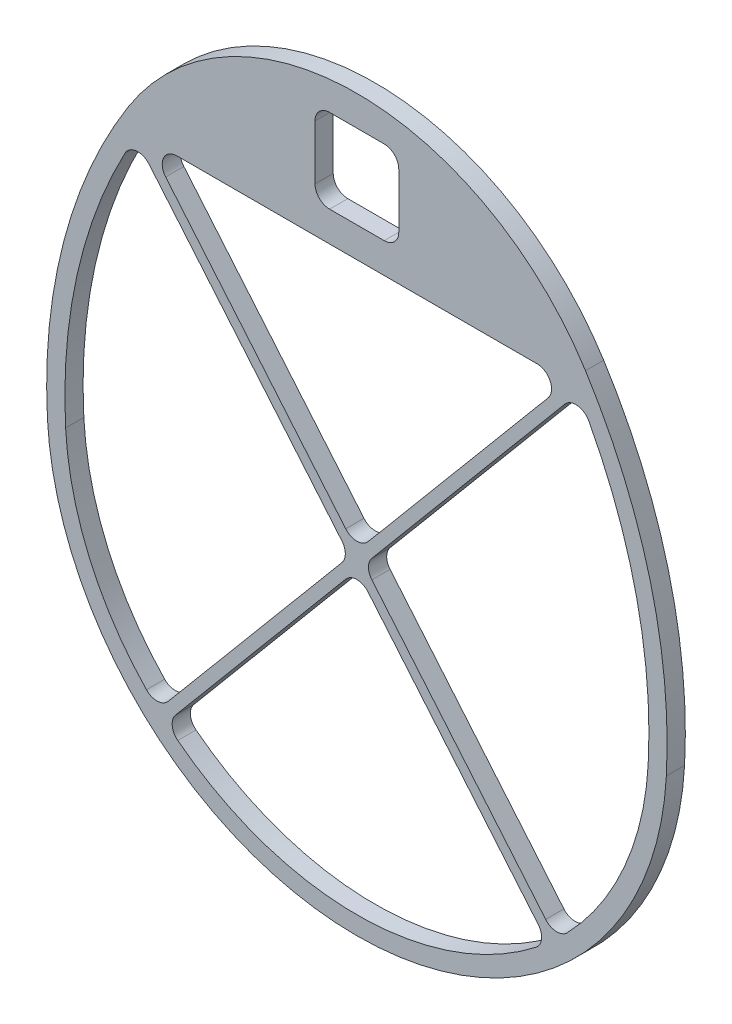
SolidWorks part; units mm, degrees
material "Balsa"
ref_plane "Front Plane" through (0, 0, 0) normal (0, 0, 1) x (1, 0, 0)
ref_plane "Top Plane" through (0, 0, 0) normal (0, 1, 0) x (1, 0, 0)
ref_plane "Right Plane" through (0, 0, 0) normal (1, 0, 0) x (0, 0, -1)
sketch "Sketch1" plane through (0, 0, 0) normal (0, 0, 1) x (1, 0, 0)
  line L8 (-101.6, 0) -> (101.6, 0) construction
  line L9 (-79.7395, 107.95) -> (79.7395, 107.95)
  line L10 (-76.2, 101.6) -> (76.2, 101.6)
  line L21 (-107.9408, -0.3425) -> (-101.6, 0)
  line L22 (101.6, 0) -> (107.9408, -0.3425)
  arc A0 (76.2, 101.6) -> (101.6, 0) centre (-75.9412, 9.5897) cw
  arc A1 (-76.2, 101.6) -> (-101.6, 0) centre (75.9412, 9.5897) ccw
  arc A2 (-79.7395, 107.95) -> (-107.9408, -0.3425) centre (75.9412, 9.5897) ccw
  arc A3 (79.7395, 107.95) -> (107.9408, -0.3425) centre (-75.9412, 9.5897) cw
  arc A4 (-81.6336, 104.8861) -> (-107.9408, -0.3425) centre (75.9412, 9.5897) ccw construction
  arc A5 (81.6336, 104.8861) -> (107.9408, -0.3425) centre (-75.9412, 9.5897) cw construction
  arc A6 (76.2, 101.6) -> (101.6, 0) centre (-75.9412, 9.5897) cw construction
  arc A7 (-76.2, 101.6) -> (-101.6, 0) centre (75.9412, 9.5897) ccw construction
  arc A8 (-79.7395, 107.95) -> (79.7395, 107.95) centre (0, 57.57) cw
  arc A9 (-101.6, 0) -> (101.6, 0) centre (0, 5.4878) ccw
  arc A10 (-107.9408, -0.3425) -> (107.9408, -0.3425) centre (0, 5.4878) ccw
  point P0 (0, 0)
  point P13 (0, 101.6)
  dimension "D7" = 203.2
  dimension "D2" = 177.8
  dimension "D3" = 101.6
  dimension "D6" = 152.4
  dimension "D1" = 6.35
  dimension "D4" = 6.35
  dimension "D5" = 6.35
extrude "Boss-Extrude1" add sketch "Sketch1" along normal blind 6.35
sketch "Sketch2" plane through (0, 0, 6.35) normal (0, 0, 1) x (1, 0, 0)
  line L0 (0, 101.6) -> (0, 151.8914) construction
  line L1 (-14.605, 141.3507) -> (14.605, 141.3507)
  line L2 (-14.605, 141.3507) -> (-14.605, 112.1407)
  line L3 (-14.605, 112.1407) -> (14.605, 112.1407)
  line L4 (14.605, 141.3507) -> (14.605, 112.1407)
  line L5 (-14.605, 141.3507) -> (14.605, 112.1407) construction
  line L6 (-14.605, 112.1407) -> (14.605, 141.3507) construction
  line L7 (-76.2, 101.6) -> (76.2, 101.6) construction
  arc A0 (79.7395, 107.95) -> (-79.7395, 107.95) centre (0, 57.57) ccw construction
  point P0 (0, 126.7457)
  point P15 (0, 126.7457)
  dimension "D1" = 29.21
  dimension "D2" = 29.21
extrude "Cut-Extrude1" cut sketch "Sketch2" against normal up to next
fillet "Fillet1" radius 5.08 4 edges at (14.605, 112.1407, 3.175) (14.605, 141.3507, 3.175) (-14.605, 141.3507, 3.175) (-14.605, 112.1407, 3.175)
sketch "Sketch3" plane through (0, 0, 6.35) normal (0, 0, 1) x (1, 0, 0)
  line L0 (-77.6593, 100.3755) -> (69.2819, -74.7423)
  line L1 (-77.6593, 100.3755) -> (-74.7407, 102.8245)
  line L2 (69.2819, -74.7423) -> (72.2006, -72.2932)
  line L3 (-74.7407, 102.8245) -> (72.2006, -72.2932)
  line L4 (-76.2, 101.6) -> (76.2, 101.6) construction
  line L5 (74.7407, 102.8245) -> (-72.2006, -72.2932)
  line L6 (74.7407, 102.8245) -> (77.6593, 100.3755)
  line L7 (-72.2006, -72.2932) -> (-69.2819, -74.7423)
  line L8 (77.6593, 100.3755) -> (-69.2819, -74.7423)
  point P0 (76.2, 101.6)
  point P3 (-76.2, 101.6)
  point P15 (0, 0)
  arc M17 (101.6, 0) -> (-101.6, 0) centre (0, 5.4878) cw
  arc M18 (-101.6, 0) -> (-76.2, 101.6) centre (75.9412, 9.5897) cw
  line M19 (-76.2, 101.6) -> (76.2, 101.6)
  arc M20 (76.2, 101.6) -> (101.6, 0) centre (-75.9412, 9.5897) cw
  dimension "D1" = 3.81
  dimension "D2" = 50
  dimension "D3" = 228.6
  dimension "D4" = 3.81
  dimension "D5" = 50
  dimension "D6" = 228.6
extrude "Boss-Extrude2" add sketch "Sketch3" against normal up to surface (6.35 mm away) contours L8 L5 L3 M20 M19 | L5 L3 L0 M19 M18 | L3 L8 L0 M17 | L8 L0 L5 L7 | L8 L3 L5 L0 up to face at (0, 126.7457, 0)
fillet "Fillet2" radius 5.08 12 edges at (73.7132, 101.6, 3.175) (0, 13.752, 3.175) (-2.4868, 10.7884, 3.175) (0, 7.8247, 3.175) (66.546, -71.4817, 3.175) (-77.2338, 99.8684, 3.175) (2.4868, 10.7884, 3.175) (77.2338, 99.8684, 3.175) (69.3826, -68.9349, 3.175) (-73.7132, 101.6, 3.175) (-69.3826, -68.9349, 3.175) (-66.546, -71.4817, 3.175)
